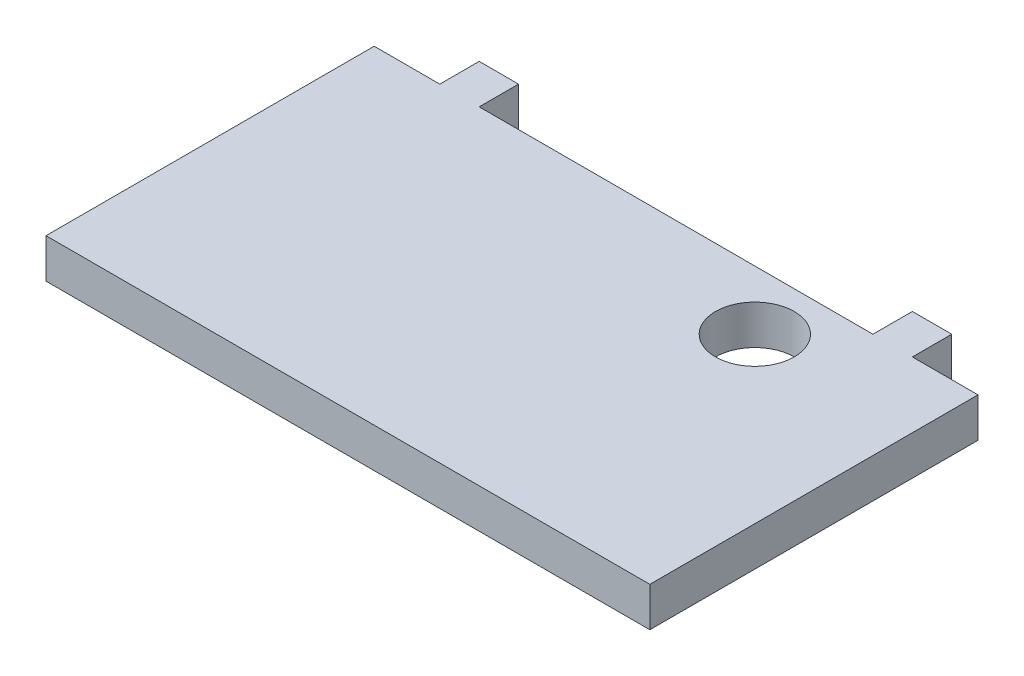
SolidWorks part; units mm, degrees
material "Pine"
ref_plane "정면" through (0, 0, 0) normal (0, 0, 1) x (1, 0, 0)
ref_plane "윗면" through (0, 0, 0) normal (0, 1, 0) x (1, 0, 0)
ref_plane "우측면" through (0, 0, 0) normal (1, 0, 0) x (0, 0, -1)
sketch "Sketch1" plane through (0, 0, 0) normal (0, 0, 1) x (1, 0, 0)
  line L0 (0, -18.5254) -> (0, 26.4304) construction
  line L1 (-46, 0) -> (46, 0)
  line L2 (-46, 0) -> (-46, 6)
  line L3 (-46, 6) -> (46, 6)
  line L4 (46, 6) -> (46, 0)
  dimension "D1" = 92
  dimension "D2" = 6
  dimension "D3" = 46
extrude "Boss-Extrude1" add sketch "Sketch1" along normal blind 50
sketch "Sketch2" plane through (0, 0, 0) normal (0, 0, -1) x (-1, 0, 0)
  line L0 (-36, 0) -> (-36, 6)
  line L1 (46, 0) -> (-46, 0) construction
  line L2 (-46, 6) -> (46, 6) construction
  line L3 (-36, 6) -> (-30, 6)
  line L4 (-30, 6) -> (-30, 0)
  line L5 (-30, 0) -> (-36, 0)
  line L6 (-46, 0) -> (-46, 6) construction
  line L7 (0, -3.4113) -> (0, 11.4135) construction
  line L8 (30, 0) -> (36, 0)
  line L9 (30, 6) -> (30, 0)
  line L10 (36, 6) -> (30, 6)
  line L11 (36, 0) -> (36, 6)
  line L12 (46, 6) -> (46, 0) construction
  dimension "D1" = 6
  dimension "D2" = 6
  dimension "D3" = 10
  dimension "D4" = 10
extrude "Boss-Extrude2" add sketch "Sketch2" along normal blind 6
sketch "Sketch3" plane through (0, 0, 0) normal (0, -1, 0) x (1, 0, 0)
  line L0 (46, 50) -> (46, 0) construction
  line L1 (-30, 0) -> (30, 0) construction
  circle A0 centre (21, 9) radius 6
  dimension "D1" = 25
  dimension "D2" = 9
extrude "Cut-Extrude1" cut sketch "Sketch3" against normal blind 6 contours A0
